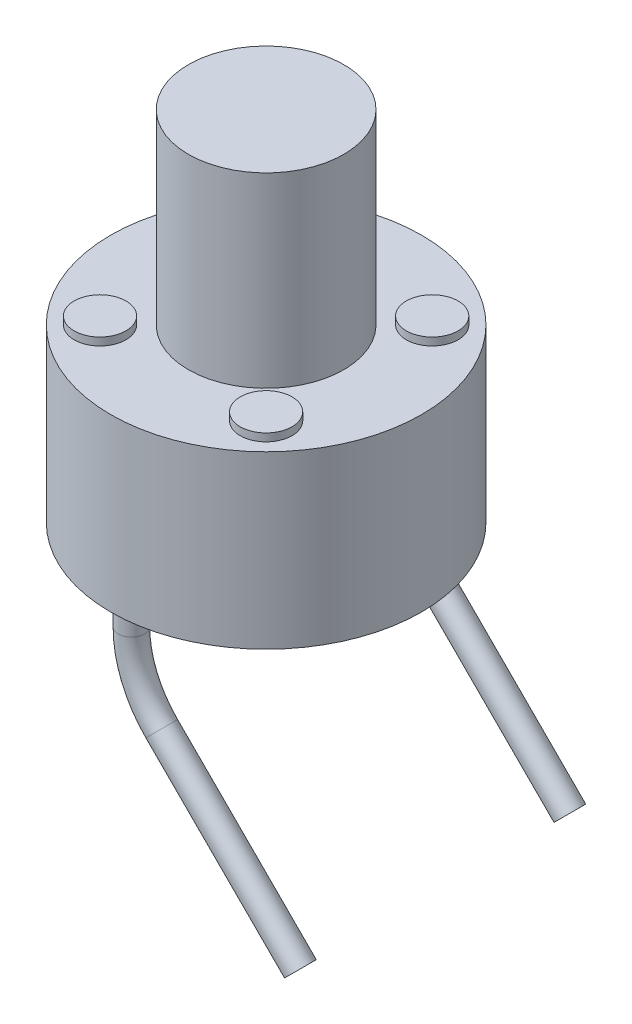
SolidWorks part; units mm, degrees
ref_plane "Front Plane" through (0, 0, 0) normal (0, 0, 1) x (1, 0, 0)
ref_plane "Top Plane" through (0, 0, 0) normal (0, 1, 0) x (1, 0, 0)
ref_plane "Right Plane" through (0, 0, 0) normal (1, 0, 0) x (0, 0, -1)
sketch "Sketch1" plane through (0, 0, 0) normal (0, 1, 0) x (1, 0, 0)
  circle A0 centre (0, 0) radius 3
  dimension "D1" = 6
extrude "Boss-Extrude1" add sketch "Sketch1" along normal blind 3.3
sketch "Sketch5" plane through (0, 0, 0) normal (0, 0, 1) x (1, 0, 0)
  line L0 (0, 0) -> (0, -0.4421)
  line L1 (0.5858, -1.8563) -> (3.2615, -4.532)
  arc A0 (0, -0.4421) -> (0.5858, -1.8563) centre (2, -0.4421) ccw
  point P5 (0, -1.2705)
  dimension "D2" = 2
  dimension "D1" = 45
sketch "Sketch2" plane through (0, 3.3, 0) normal (0, 1, 0) x (1, 0, 0)
  circle A0 centre (0, 0) radius 1.5
  dimension "D1" = 3
extrude "Boss-Extrude2" add sketch "Sketch2" along normal blind 3.6
sketch "Sketch3" plane through (0, 0, 0) normal (0, -1, 0) x (1, 0, 0)
  circle A0 centre (0, 2.6) radius 0.25
  circle A1 centre (0, -2.6) radius 0.25
  dimension "D1" = 0.5
  dimension "D2" = 2.6
  dimension "D3" = 2.6
sketch "Sketch4" plane through (0, 3.3, 0) normal (0, 1, 0) x (1, 0, 0)
  line L1 (1.6027, -1.6027) -> (-1.6027, -1.6027) construction
  line L2 (1.6027, -1.6027) -> (1.6027, 1.6027) construction
  line L3 (1.6027, 1.6027) -> (-1.6027, 1.6027) construction
  line L4 (-1.6027, -1.6027) -> (-1.6027, 1.6027) construction
  line L5 (0, 1.6027) -> (0, -1.6027) construction
  line L6 (1.6027, 0) -> (-1.6027, 0) construction
  circle A0 centre (-1.6027, 1.6027) radius 0.5
  circle A1 centre (1.6027, 1.6027) radius 0.5
  circle A2 centre (-1.6027, -1.6027) radius 0.5
  circle A3 centre (1.6027, -1.6027) radius 0.5
  point P0 (0, 0)
  dimension "D1" = 1
extrude "Boss-Extrude4" add sketch "Sketch4" along normal blind 0.15
ref_point "Point1"
sweep "Sweep2" add profiles "Sketch3" path "Sketch5"
